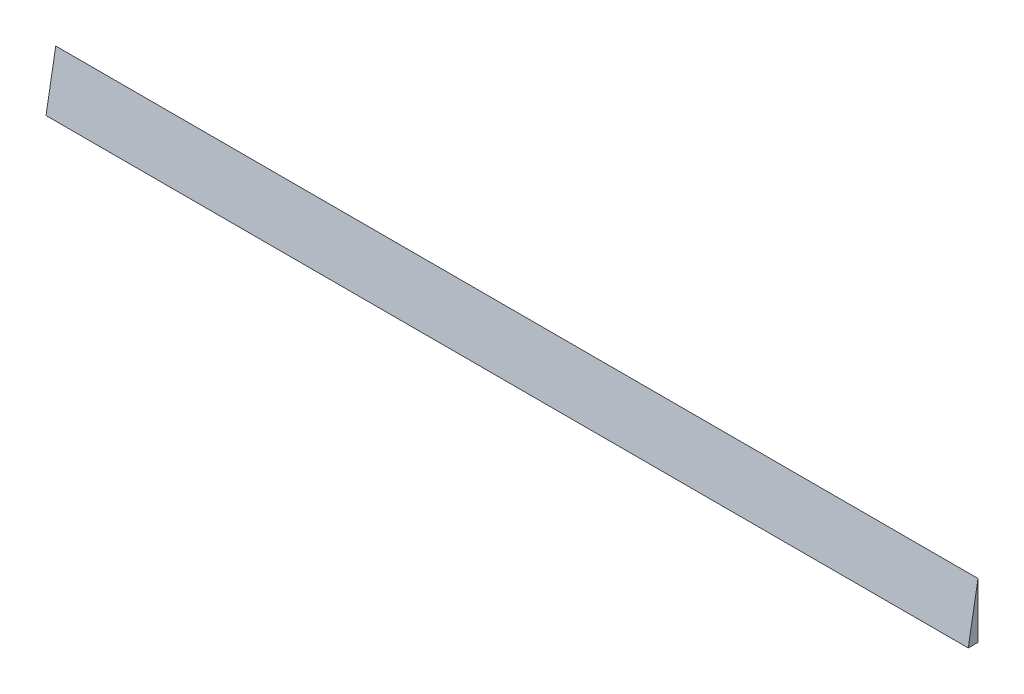
SolidWorks part; units mm, degrees
ref_plane "Front Plane" through (0, 0, 0) normal (0, 0, 1) x (1, 0, 0)
ref_plane "Top Plane" through (0, 0, 0) normal (0, 1, 0) x (1, 0, 0)
ref_plane "Right Plane" through (0, 0, 0) normal (1, 0, 0) x (0, 0, -1)
sketch "Sketch1" plane through (0, 0, 0) normal (1, 0, 0) x (0, 0, -1)
  line L0 (0, 0) -> (0, 24)
  line L1 (0, 24) -> (-4.2318, 0)
  line L2 (-4.2318, 0) -> (0, 0)
  dimension "D1" = 24
  dimension "D2" = 80
extrude "Boss-Extrude1" add sketch "Sketch1" along normal blind 400
